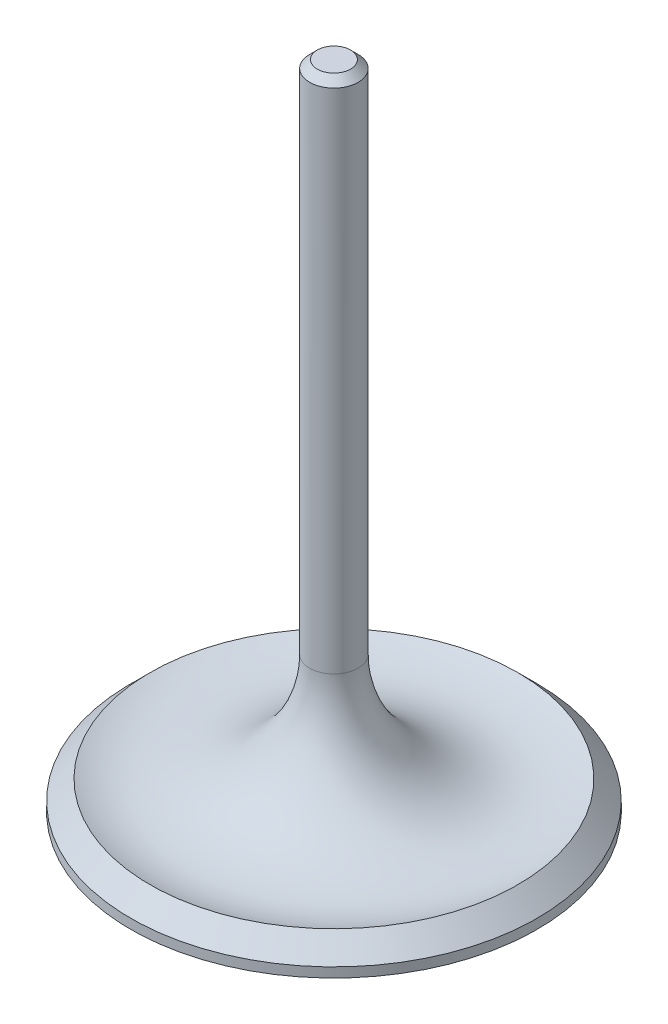
SolidWorks part; units mm, degrees
ref_plane "Front Plane" through (0, 0, 0) normal (0, 0, 1) x (1, 0, 0)
ref_plane "Top Plane" through (0, 0, 0) normal (0, 1, 0) x (1, 0, 0)
ref_plane "Right Plane" through (0, 0, 0) normal (1, 0, 0) x (0, 0, -1)
sketch "Sketch1" plane through (0, 0, 0) normal (0, 0, 1) x (1, 0, 0)
  line L0 (0, 0) -> (0, 85.55)
  line L1 (0, 85.55) -> (3.18, 85.55)
  line L2 (3.18, 85.55) -> (3.18, 17.9547)
  line L3 (24.13, 3.81) -> (26.67, 1.27)
  line L4 (26.67, 1.27) -> (26.67, 0)
  line L5 (26.67, 0) -> (0, 0)
  arc A0 (3.18, 17.9547) -> (24.13, 3.81) centre (18.43, 17.9547) ccw
  dimension "D7" = 15.25
  dimension "D1" = 85.55
  dimension "D2" = 26.67
  dimension "D3" = 3.18
  dimension "D4" = 1.27
  dimension "D5" = 3.81
  dimension "D6" = 45
revolve "Revolve1" add sketch "Sketch1" angle 360 about L0
chamfer "Chamfer1" distance 1 angle 45 1 edges at (0, 85.55, -3.18)
